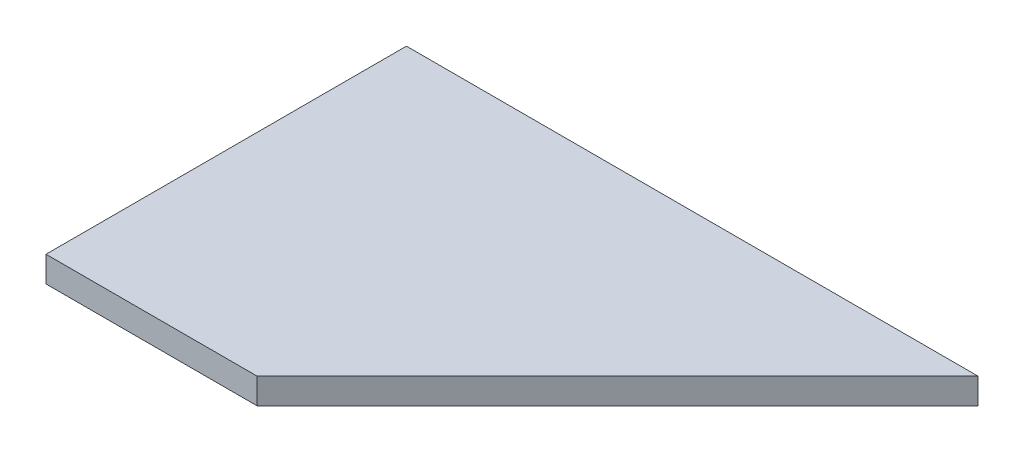
SolidWorks part; units mm, degrees
ref_plane "Front Plane" through (0, 0, 0) normal (0, 0, 1) x (1, 0, 0)
ref_plane "Top Plane" through (0, 0, 0) normal (0, 1, 0) x (1, 0, 0)
ref_plane "Right Plane" through (0, 0, 0) normal (1, 0, 0) x (0, 0, -1)
sketch "Sketch1" plane through (0, 0, 0) normal (0, 1, 0) x (1, 0, 0)
  line L0 (33.3, 21) -> (-8.7, -21)
  line L1 (-33.3, 21) -> (33.3, 21)
  line L2 (-33.3, 21) -> (-33.3, -21)
  line L3 (-33.3, -21) -> (-8.7, -21)
  point P1 (0, 0)
  dimension "D1" = 66.6
  dimension "D2" = 42
  dimension "D3" = 24.6
  dimension "D4" = 45
  dimension "D5" = 59.397
extrude "Boss-Extrude1" add sketch "Sketch1" along normal blind 3
